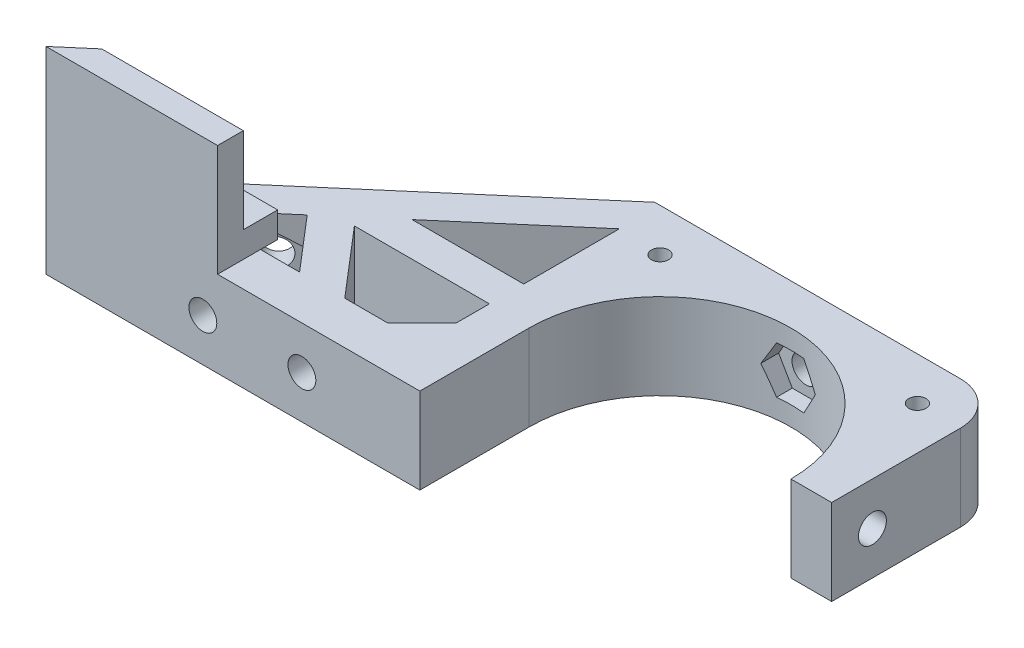
SolidWorks part; units mm, degrees
ref_plane "Alzado" through (0, 0, 0) normal (0, 0, 1) x (1, 0, 0)
ref_plane "Planta" through (0, 0, 0) normal (0, 1, 0) x (1, 0, 0)
ref_plane "Vista lateral" through (0, 0, 0) normal (1, 0, 0) x (0, 0, -1)
sketch "Croquis1" plane through (0, 0, 0) normal (0, 1, 0) x (1, 0, 0)
  line L0 (0, 20) -> (0, -20) construction
  line L1 (-20, 20) -> (20, 20)
  line L2 (-20, 20) -> (-20, -20)
  line L3 (-20, -20) -> (20, -20)
  line L4 (20, 20) -> (20, -20)
  line L5 (-20, 20) -> (20, -20) construction
  line L6 (-20, -20) -> (20, 20) construction
  line L7 (-20, -4.25) -> (-30, -7.25)
  line L8 (-30, -7.25) -> (-30, -15.25)
  line L9 (-30, -15.25) -> (30, -15.25)
  line L10 (20, -4.25) -> (30, -7.25)
  line L11 (30, -7.25) -> (30, -15.25)
  circle A0 centre (-15, 15) radius 2.125
  circle A1 centre (15, 15) radius 2.125
  circle A4 centre (0, 0) radius 15.25
  circle A5 centre (-15, -15) radius 2.125 [skipped]
  circle A6 centre (15, -15) radius 2.125 [skipped]
  point P0 (0, 0)
  point P25 (0, -15.25)
  dimension "D3" = 4.25
  dimension "D7" = 30.5
  dimension "D1" = 40
  dimension "D2" = 40
  dimension "D4" = 5
  dimension "D5" = 2
  dimension "D8" = 8
  dimension "D9" = 10
  dimension "D10" = 15.25
  dimension "D12" = 3
  dimension "D6" = 2
extrude "Soporte caja reductora" add sketch "Croquis1" against normal blind 20
sketch "Croquis3" plane through (0, 0, 15.25) normal (0, 0, 1) x (1, 0, 0)
  line L3 (-20, -20) -> (-20, 0) construction
  circle A0 centre (-23.5, -10) radius 2.125
  circle A1 centre (23.5, -10) radius 2.125
  dimension "D1" = 4.25
  dimension "D2" = 3.5
extrude "Cortar-Extruir1" cut sketch "Croquis3" against normal through all
fillet "Redondeo1" radius 5 2 edges at (-20, -10, -20) (20, -10, -20)
sketch "Sketch1" plane through (0, 0, 0) normal (0, 1, 0) x (1, 0, 0)
  line L0 (15, 20) -> (30, 20)
  line L1 (30, 20) -> (30, 8)
  line L2 (30, 8) -> (25.5, 8)
  line L4 (25.5, 8) -> (25.5, 15)
  line L5 (25.5, 15) -> (20, 15)
  circle A0 centre (15, 15) radius 5
  arc M37 (20, 15) -> (15, 20) centre (15, 15) ccw
  dimension "D1" = 12
  dimension "D2" = 5.5
extrude "Boss-Extrude1" add sketch "Sketch1" along direction (0, 1, 0) on the side against the normal up to surface (20 mm away) contours L5 L4 L2 L1 L0 M37
sketch "Sketch2" plane through (0, 0, -20) normal (0, 0, -1) x (-1, 0, 0)
  line L1 (-20, -20) -> (-20, 0) construction
  circle A0 centre (-22.75, -10) radius 1.625
  dimension "D1" = 3.25
  dimension "D2" = 2.75
extrude "Cut-Extrude1" cut sketch "Sketch2" against normal up to next
sketch "Sketch3" plane through (0, 0, -15) normal (0, 0, 1) x (1, 0, 0)
  line L1 (20, -11.5877) -> (22.75, -13.1754)
  line L2 (22.75, -13.1754) -> (25.5, -11.5877)
  line L3 (25.5, -11.5877) -> (25.5, -8.4123)
  line L4 (25.5, -8.4123) -> (22.75, -6.8246)
  line L5 (22.75, -6.8246) -> (20, -8.4123)
  line L6 (20, -8.4123) -> (20, -11.5877)
  circle A0 centre (22.75, -10) radius 2.75 construction
  dimension "D1" = 5.5
extrude "Cut-Extrude2" cut sketch "Sketch3" against normal blind 2
sketch "Sketch4" plane through (25.5, 0, 0) normal (-1, 0, 0) x (0, 0, 1)
  line L5 (-15, -8.4123) -> (-15, 0) construction
  line L6 (-20, 0) -> (-8, 0) construction
  circle A0 centre (-12.25, -10) radius 1.625
  dimension "D1" = 2.75
  dimension "D2" = 3.25
  dimension "D3" = 10
extrude "Cut-Extrude3" cut sketch "Sketch4" against normal through all
sketch "Sketch5" plane through (30, 0, 0) normal (1, 0, 0) x (0, 0, -1)
  line L1 (15, -11.5877) -> (15, -8.4123)
  line L2 (15, -8.4123) -> (12.25, -6.8246)
  line L3 (12.25, -6.8246) -> (9.5, -8.4123)
  line L4 (9.5, -8.4123) -> (9.5, -11.5877)
  line L5 (9.5, -11.5877) -> (12.25, -13.1754)
  line L6 (12.25, -13.1754) -> (15, -11.5877)
  circle A0 centre (12.25, -10) radius 2.75 construction
  dimension "D1" = 5.5
extrude "Cut-Extrude4" cut sketch "Sketch5" along normal blind 2 from surface
sketch "Croquis6" plane through (0, 0, 0) normal (0, 1, 0) x (1, 0, 0)
  line L0 (-20, -20) -> (20, -20) construction
  line L1 (-15.25, 0) -> (15.25, 0)
  line L2 (-15.25, 0) -> (-15.25, -20)
  line L3 (-15.25, -20) -> (15.25, -20)
  line L4 (15.25, 0) -> (15.25, -20)
  line L6 (-20, -20) -> (20, -20)
  line L7 (-20, -20) -> (-20, -15.25)
  line L8 (-20, -15.25) -> (20, -15.25)
  line L9 (20, -20) -> (20, -15.25)
  circle A0 centre (0, 0) radius 15.25 construction
  circle M5 centre (0, 0) radius 15.25
  line M14 (-20, -15.25) -> (-20, -20)
  line M15 (-20, -20) -> (20, -20)
  line M16 (20, -20) -> (20, -15.25)
extrude "Cortar-Extruir17" cut sketch "Croquis6" against normal through all contours L8 L2 L4 M15 | L8 L2 M14 M15 | L2 L8 M5 | L8 L4 M5 | L8 L4 M15 M16
mirror "Simetría1" about plane through (0, 0, 0) normal (0, 1, 0) of bodies 111
sketch "Croquis7" plane through (0, 0, -20) normal (0, 0, -1) x (-1, 0, 0)
  line L1 (-30, 0) -> (30, 0)
  line L2 (-30, 0) -> (-30, -20)
  line L3 (-30, -20) -> (30, -20)
  line L4 (30, 0) -> (30, -20)
extrude "Cortar-Extruir18" cut sketch "Croquis7" against normal through all
sketch "Croquis8" plane through (0, 20, 0) normal (0, 1, 0) x (1, 0, 0)
  line L3 (-15, 20) -> (30, 20) construction
  line L4 (-11.0405, 13.9391) -> (-10.3152, 11.2321)
  line L5 (10.8174, 13.8793) -> (10.3152, 11.2321)
  line L59 (10.8174, 13.8793) -> (11.9787, 20)
  line L60 (-11.0405, 13.9391) -> (-12.6645, 20)
  line L61 (11.9787, 20) -> (-12.6645, 20)
  circle A0 centre (0, 0) radius 15.25
extrude "Saliente-Extruir2" add sketch "Croquis8" along normal blind 49
sketch "Croquis9" plane through (0, 69, 0) normal (0, 1, 0) x (1, 0, 0)
  line L0 (-20, 0) -> (20, 0)
  line L1 (-20, 15) -> (-20, -4.25) construction
  line L2 (20, 15) -> (20, -4.25) construction
  line L3 (-20, 0) -> (-20, 15)
  line L4 (-15, 20) -> (12.6645, 20)
  line L5 (12.6645, 20) -> (20, 13.9368)
  line L6 (20, 13.9368) -> (20, 0)
  line L7 (20, 0) -> (20.1759, -0.147)
  line L8 (-14.75, 0) -> (-14.75, -15.25)
  line L9 (-15.25, -15.25) -> (-30, -15.25)
  line L10 (-30, -15.25) -> (-30, -7.25)
  line L11 (-30, -7.25) -> (-20, -4.25)
  line L12 (-20, -4.25) -> (-20, 0)
  line L13 (-14.75, -15.25) -> (-15.25, -15.25)
  line L14 (-14.75, -15.25) -> (0, -15.25)
  line L15 (0, -15.25) -> (0, -14.75)
  circle A0 centre (0, 0) radius 14.75
  circle A1 centre (-15, 15) radius 5
  dimension "D1" = 29.5
extrude "Soporte motor" add sketch "Croquis9" against normal blind 15 from offset 15 offset against normal yes
sketch "Croquis12" plane through (0, 0, 15.25) normal (0, 0, 1) x (1, 0, 0)
  line L1 (0, 54) -> (-30, 54) construction
  line L2 (-20, 39) -> (-20, 54) construction
  circle A0 centre (-23.5, 46.5) radius 2.125
  dimension "D3" = 4.25
  dimension "D1" = 7.5
  dimension "D2" = 3.5
extrude "Agujeros de sujecion a base" cut sketch "Croquis12" against normal through all
sketch "Croquis13" plane through (0, 0, 15.25) normal (0, 0, 1) x (1, 0, 0)
  line L1 (-20, 44.4793) -> (-20, 48.5207)
  line L2 (-20, 48.5207) -> (-23.5, 50.5415)
  line L3 (-23.5, 50.5415) -> (-27, 48.5207)
  line L4 (-27, 48.5207) -> (-27, 44.4793)
  line L5 (-27, 44.4793) -> (-23.5, 42.4585)
  line L6 (-23.5, 42.4585) -> (-20, 44.4793)
  circle A0 centre (-23.5, 46.5) radius 3.5 construction
  dimension "D1" = 7
extrude "Tuerca Agujero de sujecion a base" cut sketch "Croquis13" against normal blind 10 from offset 4 offset against normal yes
sketch "Croquis10" plane through (0, 69, 0) normal (0, 1, 0) x (1, 0, 0)
  line L0 (-10.3152, 11.2321) -> (-9.8079, 9.3388)
  line L1 (10.3152, 11.2321) -> (9.4813, 8.1201)
  circle A0 centre (0, 0) radius 14.75
  circle A1 centre (0, 0) radius 15.25
  arc M2 (-10.3152, 11.2321) -> (10.3152, 11.2321) centre (0, 0) cw
extrude "Saliente-Extruir4" add sketch "Croquis10" against normal up to surface (15 mm away) contours A0 L1 L0 M2
sketch "Croquis11" plane through (0, 0, 0) normal (0, -1, 0) x (1, 0, 0)
  line L0 (0, 0) -> (0, -12.6937) construction
  line L1 (15, -20) -> (30, -20)
  line L2 (30, -20) -> (30, 15.25)
  line L3 (30, 15.25) -> (15.25, 15.25)
  line L4 (15.25, 0) -> (15.25, 15.25) construction
  line L5 (15.25, 15.25) -> (30, 15.25) construction
  line L6 (15.25, 15.25) -> (15.25, 4.25)
  line L7 (15.25, 4.25) -> (20, 4.25)
  line L8 (20, 4.25) -> (20, -15)
  circle A0 centre (0, 0) radius 22.5
  circle A1 centre (-15, -15) radius 5
  circle A2 centre (15, -15) radius 5
  line M8 (-15, -20) -> (30, -20)
  line M9 (30, -20) -> (30, -8)
  line M10 (30, -8) -> (25.5, -8)
  line M11 (25.5, -8) -> (25.5, -15)
  line M12 (25.5, -15) -> (20, -15)
  line M14 (20, 4.25) -> (30, 7.25)
  line M15 (30, 7.25) -> (30, 15.25)
  line M16 (30, 15.25) -> (15.25, 15.25)
  line M17 (15.25, 15.25) -> (15.25, 0)
  dimension "D1" = 45
extrude "Cortar-Extruir19" cut sketch "Croquis11" against normal blind 25 contours A0 L3 L7 M14 M17 | A0 M14 M15 M16 | A2 M12 M8 M9 M10 M11
mirror "Simetría2"
sketch "Croquis14" plane through (0, 0, 15.25) normal (0, 0, 1) x (1, 0, 0)
  line L1 (-30, 20) -> (20, 20)
  line L2 (-30, 20) -> (-30, 138)
  line L3 (-30, 138) -> (20, 138)
  line L4 (20, 20) -> (20, 138)
extrude "Cortar-Extruir22" cut sketch "Croquis14" against normal through all
sketch "Croquis15" plane through (0, 0, 0) normal (0, -1, 0) x (1, 0, 0)
  line L0 (-30, 7.25) -> (-30, 15.25) construction
  line L1 (-20, 4.25) -> (-30, 4.25)
  line L2 (-20, 4.25) -> (-20, 11.25)
  line L3 (-20, 11.25) -> (-30, 11.25)
  line L4 (-30, 4.25) -> (-30, 11.25)
  line L5 (-30, 15.25) -> (-15.25, 15.25) construction
  dimension "D1" = 4
extrude "Cortar-Extruir23" cut sketch "Croquis15" against normal through all
sketch "Croquis16" plane through (0, 0, 0) normal (0, -1, 0) x (1, 0, 0)
  line L0 (-15.25, 0) -> (-15.25, 15.25) construction
  line L1 (-30, 15.25) -> (-15.25, 15.25)
  line L2 (-30, 15.25) -> (-30, 12.75)
  line L3 (-20, 12.75) -> (-15.25, 12.75)
  line L4 (-15.25, 15.25) -> (-15.25, 12.75)
  line L5 (-30, 12.75) -> (-30, 11.25)
  line L6 (-30, 11.25) -> (-20, 11.25)
  line L7 (-20, 11.25) -> (-30, 11.25) construction
  line L8 (-20, -15) -> (-20, 11.25) construction
  line L9 (-20, 11.25) -> (-20, 12.75)
  dimension "D1" = 2.5
extrude "Cortar-Extruir24" cut sketch "Croquis16" against normal through all
sketch "Croquis18" plane through (0, 0, -20) normal (0, 0, -1) x (-1, 0, 0)
  line L0 (20, 0) -> (20, 20) construction
  line L1 (-20, 0) -> (20, 0)
  line L2 (-20, 0) -> (-20, 10)
  line L3 (-20, 10) -> (20, 10)
  line L4 (20, 0) -> (20, 10)
  line L5 (15, 20) -> (-15, 20) construction
  dimension "D1" = 10
extrude "Cortar-Extruir25" cut sketch "Croquis18" against normal through all
sketch "Croquis19" plane through (0, 20, 0) normal (0, 1, 0) x (1, 0, 0)
  line L0 (-20, -12.75) -> (-34, -12.75)
  line L1 (-34, -12.75) -> (-34, -7.75)
  line L2 (-34, -7.75) -> (-24, -7.75)
  line L3 (-24, -7.75) -> (-20, -3.75)
  line L4 (-20, 15) -> (-20, -12.75) construction
  line L5 (-20, -3.75) -> (-20, -12.75)
  dimension "D1" = 5
  dimension "D2" = 4
  dimension "D3" = 4
  dimension "D4" = 10
extrude "Saliente-Extruir5" add sketch "Croquis19" against normal up to surface (10 mm away) up to face at (15, 10, -12.875)
sketch "Croquis20" plane through (0, 0, 7.75) normal (0, 0, -1) x (-1, 0, 0)
  circle A0 centre (29, 15) radius 1
  dimension "D1" = 2
extrude "Cortar-Extruir26" cut sketch "Croquis20" against normal through all
sketch "Croquis21" plane through (20, 0, 0) normal (1, 0, 0) x (0, 0, -1)
  line L1 (20, 20) -> (20, 10) construction
  circle A0 centre (4.75, 15) radius 1.625
  dimension "D1" = 3.25
  dimension "D2" = 15.25
extrude "Cortar-Extruir27" cut sketch "Croquis21" against normal up to next
sketch "Croquis22" plane through (0, 10, 0) normal (0, -1, 0) x (1, 0, 0)
  circle A0 centre (-15, -15) radius 2.125
  circle A1 centre (15, -15) radius 2.125
  circle A2 centre (15, -15) radius 1
  circle A3 centre (-15, -15) radius 1
  dimension "D1" = 2
extrude "Saliente-Extruir6" add sketch "Croquis22" against normal blind 10
sketch "Croquis23" plane through (0, 0, -20) normal (0, 0, -1) x (-1, 0, 0)
  circle A0 centre (0, 15) radius 1.625
  dimension "D1" = 3.25
extrude "Cortar-Extruir28" cut sketch "Croquis23" against normal through all
sketch "Croquis24" plane through (0, 0, -20) normal (0, 0, -1) x (-1, 0, 0)
  line L1 (1.5877, 12.25) -> (3.1754, 15)
  line L2 (3.1754, 15) -> (1.5877, 17.75)
  line L3 (1.5877, 17.75) -> (-1.5877, 17.75)
  line L4 (-1.5877, 17.75) -> (-3.1754, 15)
  line L5 (-3.1754, 15) -> (-1.5877, 12.25)
  line L6 (-1.5877, 12.25) -> (1.5877, 12.25)
  circle A0 centre (0, 15) radius 2.75 construction
  dimension "D1" = 5.5
extrude "Cortar-Extruir29" cut sketch "Croquis24" against normal blind 10 from offset 3 offset against normal yes
sketch "Croquis26" plane through (0, 10, 0) normal (0, -1, 0) x (1, 0, 0)
  line L0 (-29, 12.75) -> (-58.825, 12.75)
  line L1 (-58.825, 12.75) -> (-39.1605, -4.1045)
  line L3 (-39.5945, 1.5357) -> (-46.8449, 7.75)
  line L4 (-46.8449, 7.75) -> (-34.2682, 7.75)
  line L5 (-34.2682, 7.75) -> (-39.5945, 1.5357)
  line L7 (-29, 7.75) -> (-35.7321, -0.1045)
  line L8 (-29, 7.75) -> (-29, 12.75)
  line L9 (-34, 7.75) -> (-24, 7.75) construction
  line L10 (-34, 12.75) -> (-15.25, 12.75) construction
  line L11 (-39.1605, -4.1045) -> (-20, -4.1045)
  line L12 (-20, 3.75) -> (-20, -15) construction
  line L13 (-20, -4.1045) -> (-20, -0.1045)
  line L14 (-20, -0.1045) -> (-35.7321, -0.1045)
  dimension "D1" = 4
  dimension "D2" = 4
  dimension "D3" = 4
  dimension "D4" = 29.825
  dimension "D5" = 40.6
extrude "Saliente-Extruir7" add sketch "Croquis26" against normal blind 10
sketch "Croquis27" plane through (0, 0, 12.75) normal (0, 0, 1) x (1, 0, 0)
  line L0 (-29, 16) -> (-29, 14) construction
  line L1 (-46.8449, 20) -> (-46.8449, 10) construction
  circle A0 centre (-40.5449, 15) radius 1.625
  circle A2 centre (-29, 15) radius 1.625
  dimension "D1" = 3.25
  dimension "D2" = 6.3
extrude "Cortar-Extruir30" cut sketch "Croquis27" against normal up to next
sketch "Croquis28" plane through (0, 0, 12.75) normal (0, 0, 1) x (1, 0, 0)
  line L1 (-38.9572, 12.25) -> (-37.3694, 15)
  line L2 (-37.3694, 15) -> (-38.9572, 17.75)
  line L3 (-38.9572, 17.75) -> (-42.1326, 17.75)
  line L4 (-42.1326, 17.75) -> (-43.7203, 15)
  line L5 (-43.7203, 15) -> (-42.1326, 12.25)
  line L6 (-42.1326, 12.25) -> (-38.9572, 12.25)
  line L7 (-27.4123, 12.25) -> (-25.8246, 15)
  line L8 (-25.8246, 15) -> (-27.4123, 17.75)
  line L9 (-27.4123, 17.75) -> (-30.5877, 17.75)
  line L10 (-30.5877, 17.75) -> (-32.1754, 15)
  line L11 (-32.1754, 15) -> (-30.5877, 12.25)
  line L12 (-30.5877, 12.25) -> (-27.4123, 12.25)
  circle A0 centre (-40.5449, 15) radius 2.75 construction
  circle A1 centre (-29, 15) radius 2.75 construction
  dimension "D1" = 5.5
extrude "Cortar-Extruir31" cut sketch "Croquis28" against normal up to next from offset 3 offset against normal yes
sketch "Croquis29" plane through (-18.6128, 0, -21.716) normal (-0.6508, 0, -0.7593) x (-0.7593, 0, 0.6508)
  line L2 (31.0624, 20) -> (31.0624, 10) construction
  circle A0 centre (33.8124, 15) radius 1.625
  dimension "D2" = 3.25
  dimension "D1" = 2.75
extrude "Cortar-Extruir32" cut sketch "Croquis29" against normal up to next
sketch "Croquis31" plane through (-18.6128, 0, -21.716) normal (-0.6508, 0, -0.7593) x (-0.7593, 0, 0.6508)
  line L1 (36.5624, 16.5877) -> (33.8124, 18.1754)
  line L2 (33.8124, 18.1754) -> (31.0624, 16.5877)
  line L3 (31.0624, 16.5877) -> (31.0624, 13.4123)
  line L4 (31.0624, 13.4123) -> (33.8124, 11.8246)
  line L5 (33.8124, 11.8246) -> (36.5624, 13.4123)
  line L6 (36.5624, 13.4123) -> (36.5624, 16.5877)
  circle A0 centre (33.8124, 15) radius 2.75 construction
  dimension "D1" = 5.5
extrude "Cortar-Extruir33" cut sketch "Croquis31" against normal up to next from offset 2.5 offset against normal yes
sketch "Croquis35" plane through (0, 20, 0) normal (0, 1, 0) x (1, 0, 0)
  line L0 (-15, 20) -> (15, 20) construction
  line L1 (10.3896, 0) -> (23.695, 0)
  line L2 (10.3896, 0) -> (10.3896, -6.8269)
  line L3 (10.3896, -6.8269) -> (23.695, -6.8269)
  line L4 (23.695, 0) -> (23.695, -6.8269)
  dimension "D1" = 20
extrude "Cortar-Extruir34" cut sketch "Croquis35" against normal through all both and the other way through all
sketch "Croquis36" plane through (20, 0, 0) normal (1, 0, 0) x (0, 0, -1)
  line L1 (7.5, 16.5877) -> (4.75, 18.1754)
  line L2 (4.75, 18.1754) -> (2, 16.5877)
  line L3 (2, 16.5877) -> (2, 13.4123)
  line L4 (2, 13.4123) -> (4.75, 11.8246)
  line L5 (4.75, 11.8246) -> (7.5, 13.4123)
  line L6 (7.5, 13.4123) -> (7.5, 16.5877)
  circle A0 centre (4.75, 15) radius 2.75 construction
  dimension "D1" = 5.5
extrude "Cortar-Extruir35" cut sketch "Croquis36" against normal blind 10 from offset 3 offset against normal yes
sketch "Croquis37" plane through (0, 10, 0) normal (0, -1, 0) x (1, 0, 0)
  line L0 (-39.1605, -4.1045) -> (-20.6149, -20)
  line L1 (-20.6149, -20) -> (-15, -20)
  line L2 (-33.014, -4.1045) -> (-19.5581, -15.6376)
  line L3 (-39.1605, -4.1045) -> (-20, -4.1045) construction
  line L4 (-19.5581, -15.6376) -> (-15, -20)
  line L5 (-58.825, 12.75) -> (-39.1605, -4.1045) construction
  line L6 (-39.5945, 1.5357) -> (-46.8449, 7.75) construction
  line L7 (-39.1605, -4.1045) -> (-33.014, -4.1045)
extrude "Saliente-Extruir8" add sketch "Croquis37" against normal blind 10
sketch "Croquis38" plane through (0, 10, 0) normal (0, -1, 0) x (1, 0, 0)
  line L0 (-58.825, 12.75) -> (-38.825, 12.75)
  line L1 (-58.825, 12.75) -> (-15.25, 12.75) construction
  line L2 (-38.825, 12.75) -> (-38.825, 9.75)
  line L3 (-38.825, 9.75) -> (-55.3248, 9.75)
  line L4 (-58.825, 12.75) -> (-20.6149, -20) construction
  line L5 (-55.3248, 9.75) -> (-58.825, 12.75)
  dimension "D1" = 3
  dimension "D2" = 20
extrude "Saliente-Extruir9" add sketch "Croquis38" along normal blind 13
sketch "Croquis39" plane through (0, 10, 0) normal (0, -1, 0) x (1, 0, 0)
  line L0 (-38.825, 9.75) -> (-38.825, 7.75)
  line L1 (-46.8449, 7.75) -> (-34.2682, 7.75) construction
  line L3 (-55.3248, 9.75) -> (-20.6149, -20) construction
  line L4 (-52.9914, 7.75) -> (-55.3248, 9.75)
  line L5 (-55.3248, 9.75) -> (-38.825, 9.75)
  line L6 (-52.9914, 7.75) -> (-50.658, 5.75)
  line L7 (-50.658, 5.75) -> (-38.825, 5.75)
  line L8 (-38.825, 5.75) -> (-38.825, 7.75)
  point P5 (0, 0)
  dimension "D1" = 2
extrude "Saliente-Extruir10" add sketch "Croquis39" along normal blind 3
mirror "Simetría3" of bodies 142
sketch "Croquis40" plane through (0, 0, -20) normal (0, 0, -1) x (-1, 0, 0)
  line L1 (-30.8963, 20) -> (75.6873, 20)
  line L2 (-30.8963, 20) -> (-30.8963, -27.3915)
  line L3 (-30.8963, -27.3915) -> (75.6873, -27.3915)
  line L4 (75.6873, 20) -> (75.6873, -27.3915)
extrude "Cortar-Extruir36" cut sketch "Croquis40" against normal through all both and the other way through all
